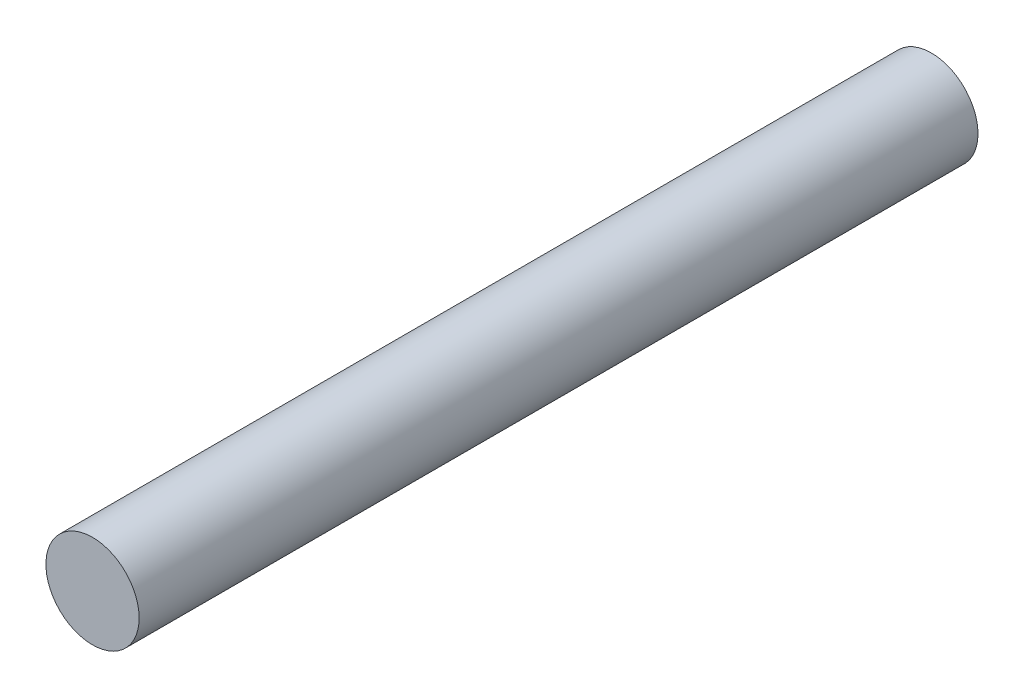
SolidWorks part; units mm, degrees
ref_plane "Front Plane" through (0, 0, 0) normal (0, 0, 1) x (1, 0, 0)
ref_plane "Top Plane" through (0, 0, 0) normal (0, 1, 0) x (1, 0, 0)
ref_plane "Right Plane" through (0, 0, 0) normal (1, 0, 0) x (0, 0, -1)
sketch "Sketch1" plane through (0, 0, 0) normal (0, 0, 1) x (1, 0, 0)
  circle A0 centre (0, 0) radius 3.175
  dimension "D1" = 6.35
extrude "Boss-Extrude1" add sketch "Sketch1" along normal blind 57.15
